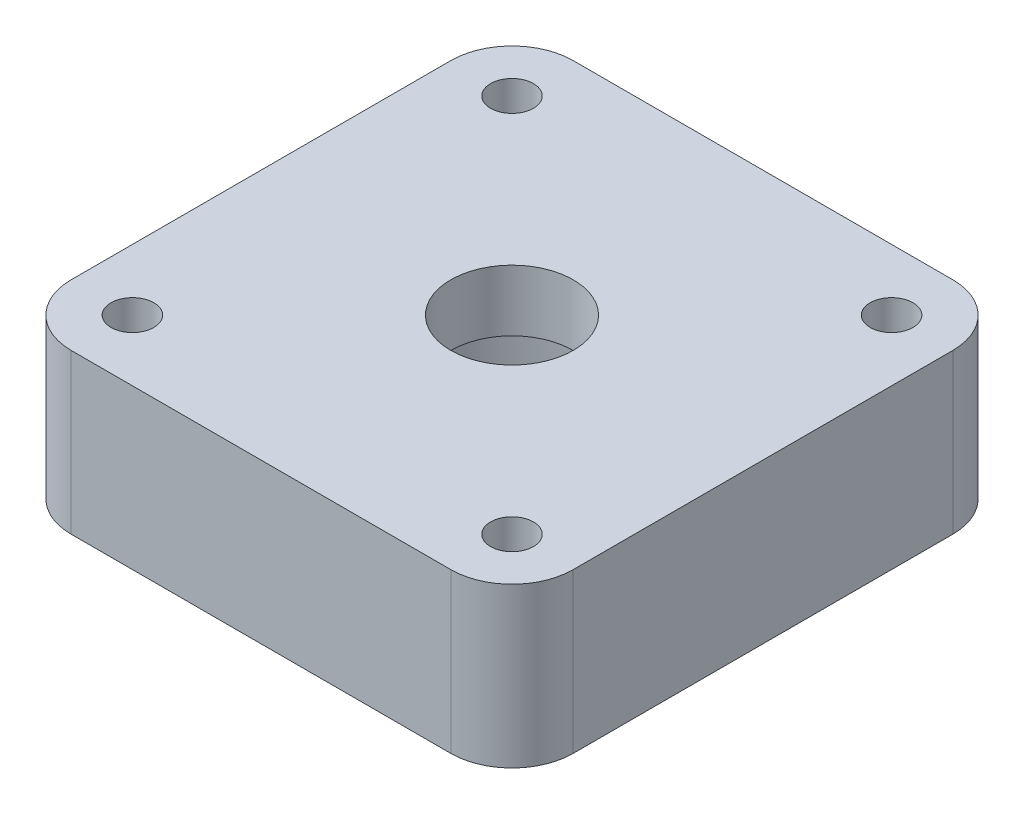
SolidWorks part; units mm, degrees
ref_plane "Front Plane" through (0, 0, 0) normal (0, 0, 1) x (1, 0, 0)
ref_plane "Top Plane" through (0, 0, 0) normal (0, 1, 0) x (1, 0, 0)
ref_plane "Right Plane" through (0, 0, 0) normal (1, 0, 0) x (0, 0, -1)
sketch "Sketch1" plane through (0, 0, 0) normal (0, 1, 0) x (1, 0, 0)
  line L1 (-15.5, 20.5) -> (15.5, 20.5)
  line L2 (-20.5, 15.5) -> (-20.5, -15.5)
  line L3 (-15.5, -20.5) -> (15.5, -20.5)
  line L4 (20.5, 15.5) -> (20.5, -15.5)
  circle A0 centre (0, 0) radius 11
  circle A1 centre (-15.5, 15.5) radius 1.75
  circle A2 centre (15.5, 15.5) radius 1.75
  circle A3 centre (15.5, -15.5) radius 1.75
  circle A4 centre (-15.5, -15.5) radius 1.75
  arc A5 (-15.5, 20.5) -> (-20.5, 15.5) centre (-15.5, 15.5) ccw
  arc A6 (20.5, 15.5) -> (15.5, 20.5) centre (15.5, 15.5) ccw
  arc A7 (15.5, -20.5) -> (20.5, -15.5) centre (15.5, -15.5) ccw
  arc A8 (-20.5, -15.5) -> (-15.5, -20.5) centre (-15.5, -15.5) ccw
  dimension "D1" = 3.5
  dimension "D2" = 31
  dimension "D3" = 31
  dimension "D4" = 15.5
  dimension "D5" = 15.5
  dimension "D6" = 5
  dimension "D7" = 5
  dimension "D8" = 5
  dimension "D9" = 5
  dimension "D10" = 22
extrude "Boss-Extrude1" add sketch "Sketch1" along normal blind 8
sketch "Sketch2" plane through (0, 8, 0) normal (0, 1, 0) x (1, 0, 0)
  line L4 (-20.5, 15.5) -> (-20.5, -15.5)
  line L5 (-15.5, -20.5) -> (15.5, -20.5)
  line L6 (20.5, -15.5) -> (20.5, 15.5)
  line L7 (15.5, 20.5) -> (-15.5, 20.5)
  line L8 (-20.5, 15.5) -> (-20.5, -15.5)
  line L9 (-15.5, -20.5) -> (15.5, -20.5)
  line L10 (20.5, -15.5) -> (20.5, 15.5)
  line L11 (15.5, 20.5) -> (-15.5, 20.5)
  circle A0 centre (-15.5, 15.5) radius 1.75 construction
  circle A1 centre (15.5, -15.5) radius 1.75 construction
  circle A2 centre (15.5, 15.5) radius 1.75 construction
  circle A3 centre (15.5, 15.5) radius 1.75
  arc A4 (-15.5, 20.5) -> (-20.5, 15.5) centre (-15.5, 15.5) ccw
  arc A5 (-20.5, -15.5) -> (-15.5, -20.5) centre (-15.5, -15.5) ccw
  arc A6 (15.5, -20.5) -> (20.5, -15.5) centre (15.5, -15.5) ccw
  arc A7 (20.5, 15.5) -> (15.5, 20.5) centre (15.5, 15.5) ccw
  arc A8 (-15.5, 20.5) -> (-20.5, 15.5) centre (-15.5, 15.5) ccw
  arc A9 (-20.5, -15.5) -> (-15.5, -20.5) centre (-15.5, -15.5) ccw
  arc A10 (15.5, -20.5) -> (20.5, -15.5) centre (15.5, -15.5) ccw
  arc A11 (20.5, 15.5) -> (15.5, 20.5) centre (15.5, 15.5) ccw
  circle A12 centre (15.5, -15.5) radius 1.75
  circle A13 centre (-15.5, 15.5) radius 1.75
  circle A14 centre (0, 0) radius 5
  circle A15 centre (-15.5, -15.5) radius 1.75
  dimension "D2" = 10
  dimension "D1" = 0
extrude "Boss-Extrude2" add sketch "Sketch2" along normal blind 5
sketch "Sketch3" plane through (0, 0, 0) normal (0, -1, 0) x (1, 0, 0)
  line L1 (-13.8607, 18.2196) -> (-17.0356, 18.2795)
  line L2 (-17.0356, 18.2795) -> (-18.6749, 15.5599)
  line L3 (-18.6749, 15.5599) -> (-17.1393, 12.7804)
  line L4 (-17.1393, 12.7804) -> (-13.9644, 12.7205)
  line L5 (-13.9644, 12.7205) -> (-12.3251, 15.4401)
  line L6 (-12.3251, 15.4401) -> (-13.8607, 18.2196)
  line L7 (12.3251, 15.5599) -> (13.8607, 12.7804)
  line L8 (13.8607, 12.7804) -> (17.0356, 12.7205)
  line L9 (17.0356, 12.7205) -> (18.6749, 15.4401)
  line L10 (18.6749, 15.4401) -> (17.1393, 18.2196)
  line L11 (17.1393, 18.2196) -> (13.9644, 18.2795)
  line L12 (13.9644, 18.2795) -> (12.3251, 15.5599)
  line L13 (13.9644, -12.7205) -> (12.3251, -15.4401)
  line L14 (12.3251, -15.4401) -> (13.8607, -18.2196)
  line L15 (13.8607, -18.2196) -> (17.0356, -18.2795)
  line L16 (17.0356, -18.2795) -> (18.6749, -15.5599)
  line L17 (18.6749, -15.5599) -> (17.1393, -12.7804)
  line L18 (17.1393, -12.7804) -> (13.9644, -12.7205)
  line L19 (-13.8607, -12.7804) -> (-17.0356, -12.7205)
  line L20 (-17.0356, -12.7205) -> (-18.6749, -15.4401)
  line L21 (-18.6749, -15.4401) -> (-17.1393, -18.2196)
  line L22 (-17.1393, -18.2196) -> (-13.9644, -18.2795)
  line L23 (-13.9644, -18.2795) -> (-12.3251, -15.5599)
  line L24 (-12.3251, -15.5599) -> (-13.8607, -12.7804)
  circle A0 centre (-15.5, 15.5) radius 2.75 construction
  circle A1 centre (15.5, 15.5) radius 2.75 construction
  circle A2 centre (15.5, -15.5) radius 2.75 construction
  circle A3 centre (-15.5, -15.5) radius 2.75 construction
  dimension "D1" = 5.5
extrude "Cut-Extrude1" cut sketch "Sketch3" against normal blind 3
